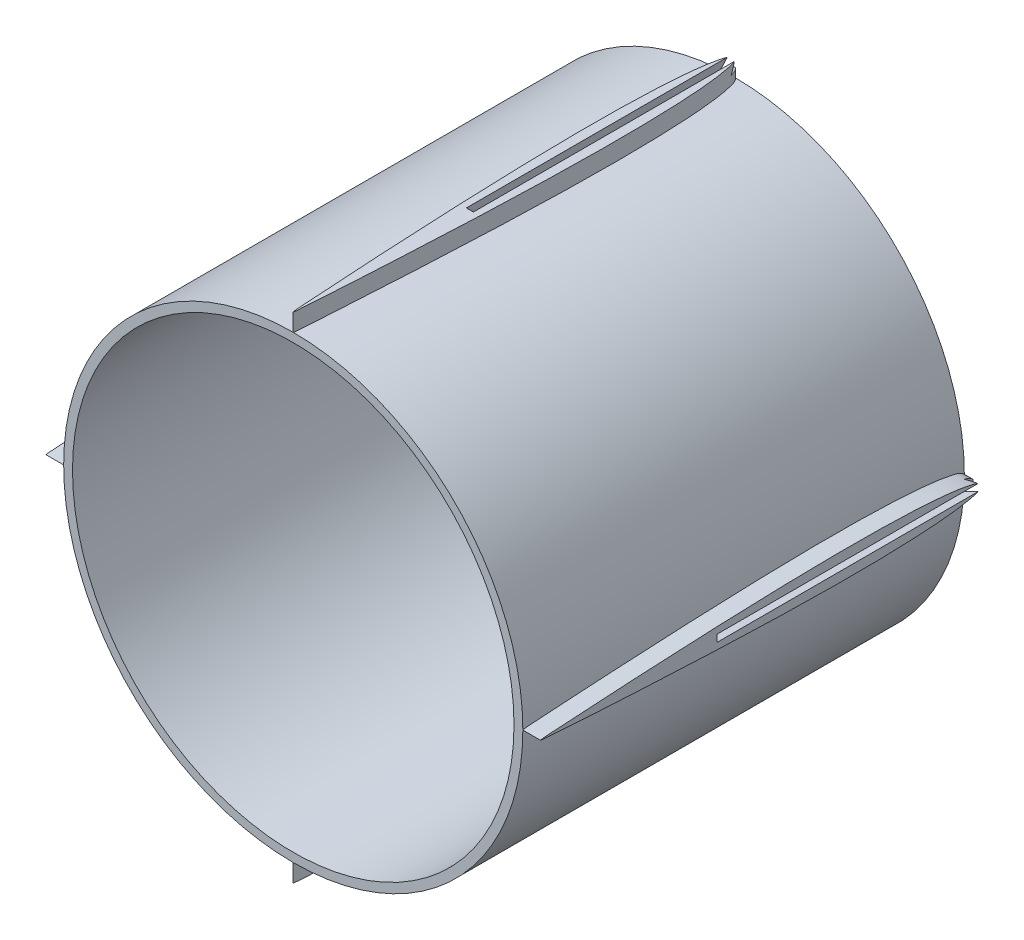
SolidWorks part; units mm, degrees
ref_plane "Front Plane" through (0, 0, 0) normal (0, 0, 1) x (1, 0, 0)
ref_plane "Top Plane" through (0, 0, 0) normal (0, 1, 0) x (1, 0, 0)
ref_plane "Right Plane" through (0, 0, 0) normal (1, 0, 0) x (0, 0, -1)
sketch "Sketch2" plane through (0, 0, 0) normal (0, 0, 1) x (1, 0, 0)
  circle A0 centre (0, 0) radius 25
  circle A1 centre (0, 0) radius 26
  dimension "D1" = 50
  dimension "D2" = 1
extrude "Boss-Extrude1" add sketch "Sketch2" along normal blind 50
curve "Curve2"
  spline degree 3 poles (-0.2116, 0, 47.1255) (0, 0, 51.4381) (0.2116, 0, 47.1255) (0.412, 0, 44.384) (0.6632, 0, 39.9273) (0.9211, 0, 35.0205) (1.1481, 0, 29.9956) (1.3323, 0, 25.0023) (1.4637, 0, 20.0003) (1.5096, 0, 15.8335) (1.4915, 0, 12.4997) (1.4421, 0, 9.9995) (1.347, 0, 7.4978) (1.2148, 0, 5.4158) (1.0548, 0, 3.7454) (0.904, 0, 2.5039) (0.6963, 0, 1.4218) (0.5125, 0, 0.6286) (0, 0, -0.3436) (-0.5125, 0, 0.6286) (-0.6963, 0, 1.4218) (-0.904, 0, 2.5039) (-1.0548, 0, 3.7454) (-1.2148, 0, 5.4158) (-1.347, 0, 7.4978) (-1.4421, 0, 9.9995) (-1.4915, 0, 12.4997) (-1.5096, 0, 15.8335) (-1.4637, 0, 20.0003) (-1.3323, 0, 25.0023) (-1.1481, 0, 29.9956) (-0.9211, 0, 35.0205) (-0.6632, 0, 39.9273) (-0.412, 0, 44.384) (-0.2116, 0, 47.1255) (0, 0, 51.4381) (0.2116, 0, 47.1255) knots -0.099682 -0.049864 -0.024947 0 0.024947 0.049864 0.099682 0.149481 0.199263 0.249028 0.298776 0.348511 0.373377 0.398248 0.423133 0.448054 0.460545 0.473081 0.485732 0.492201 0.5 0.507799 0.514268 0.526919 0.539455 0.551946 0.576867 0.601752 0.626623 0.651489 0.701224 0.750972 0.800737 0.850519 0.900318 0.950136 0.975053 1 1.024947 1.049864 1.099682 periodic
sketch "Sketch4" plane through (0, 0, 0) normal (0, 1, 0) x (1, 0, 0)
  spline S0 degree 3 poles (-0.2116, -47.1255) (0, -51.4381) (0.2116, -47.1255) (0.412, -44.384) (0.6632, -39.9273) (0.9211, -35.0205) (1.1481, -29.9956) (1.3323, -25.0023) (1.4637, -20.0003) (1.5096, -15.8335) (1.4915, -12.4997) (1.4421, -9.9995) (1.347, -7.4978) (1.2148, -5.4158) (1.0548, -3.7454) (0.904, -2.5039) (0.6963, -1.4218) (0.5125, -0.6286) (0, 0.3436) (-0.5125, -0.6286) (-0.6963, -1.4218) (-0.904, -2.5039) (-1.0548, -3.7454) (-1.2148, -5.4158) (-1.347, -7.4978) (-1.4421, -9.9995) (-1.4915, -12.4997) (-1.5096, -15.8335) (-1.4637, -20.0003) (-1.3323, -25.0023) (-1.1481, -29.9956) (-0.9211, -35.0205) (-0.6632, -39.9273) (-0.412, -44.384) (-0.2116, -47.1255) (0, -51.4381) (0.2116, -47.1255) knots -0.099682 -0.049864 -0.024947 0 0.024947 0.049864 0.099682 0.149481 0.199263 0.249028 0.298776 0.348511 0.373377 0.398248 0.423133 0.448054 0.460545 0.473081 0.485732 0.492201 0.5 0.507799 0.514268 0.526919 0.539455 0.551946 0.576867 0.601752 0.626623 0.651489 0.701224 0.750972 0.800737 0.850519 0.900318 0.950136 0.975053 1 1.024947 1.049864 1.099682 only from (0, -50) to (0, -50) construction
  spline S1 degree 3 poles (-0.2116, -47.1255) (0, -51.4381) (0.2116, -47.1255) (0.412, -44.384) (0.6632, -39.9273) (0.9211, -35.0205) (1.1481, -29.9956) (1.3323, -25.0023) (1.4637, -20.0003) (1.5096, -15.8335) (1.4915, -12.4997) (1.4421, -9.9995) (1.347, -7.4978) (1.2148, -5.4158) (1.0548, -3.7454) (0.904, -2.5039) (0.6963, -1.4218) (0.5125, -0.6286) (0, 0.3436) (-0.5125, -0.6286) (-0.6963, -1.4218) (-0.904, -2.5039) (-1.0548, -3.7454) (-1.2148, -5.4158) (-1.347, -7.4978) (-1.4421, -9.9995) (-1.4915, -12.4997) (-1.5096, -15.8335) (-1.4637, -20.0003) (-1.3323, -25.0023) (-1.1481, -29.9956) (-0.9211, -35.0205) (-0.6632, -39.9273) (-0.412, -44.384) (-0.2116, -47.1255) (0, -51.4381) (0.2116, -47.1255) knots -0.099682 -0.049864 -0.024947 0 0.024947 0.049864 0.099682 0.149481 0.199263 0.249028 0.298776 0.348511 0.373377 0.398248 0.423133 0.448054 0.460545 0.473081 0.485732 0.492201 0.5 0.507799 0.514268 0.526919 0.539455 0.551946 0.576867 0.601752 0.626623 0.651489 0.701224 0.750972 0.800737 0.850519 0.900318 0.950136 0.975053 1 1.024947 1.049864 1.099682 only from (0, -50) to (0, -50)
extrude "Boss-Extrude2" add sketch "Sketch4" against normal blind 2.5 from offset 28
sketch "Sketch5" plane through (0, 0, 0) normal (0, 0, -1) x (-1, 0, 0)
  line L0 (0, 0) -> (0, 28) construction
  line L1 (1.5005, 28) -> (-1.5005, 28) construction
  line L2 (-0.4, 28) -> (0.4, 28)
  line L3 (-0.6, 27) -> (0.6, 27)
  line L4 (-0.4, 28) -> (-0.6, 27)
  line L5 (0.6, 27) -> (0.4, 28)
  point P8 (0, 28)
  point P11 (0, 27)
  dimension "D1" = 0.8
  dimension "D2" = 1.2
  dimension "D3" = 1
extrude "Cut-Extrude1" cut sketch "Sketch5" against normal blind 30
pattern_circular "CirPattern1" count 4 over 360 about axis through (0, 0, 50) along (0, 0, -1) of "Cut-Extrude1", "Boss-Extrude2"
